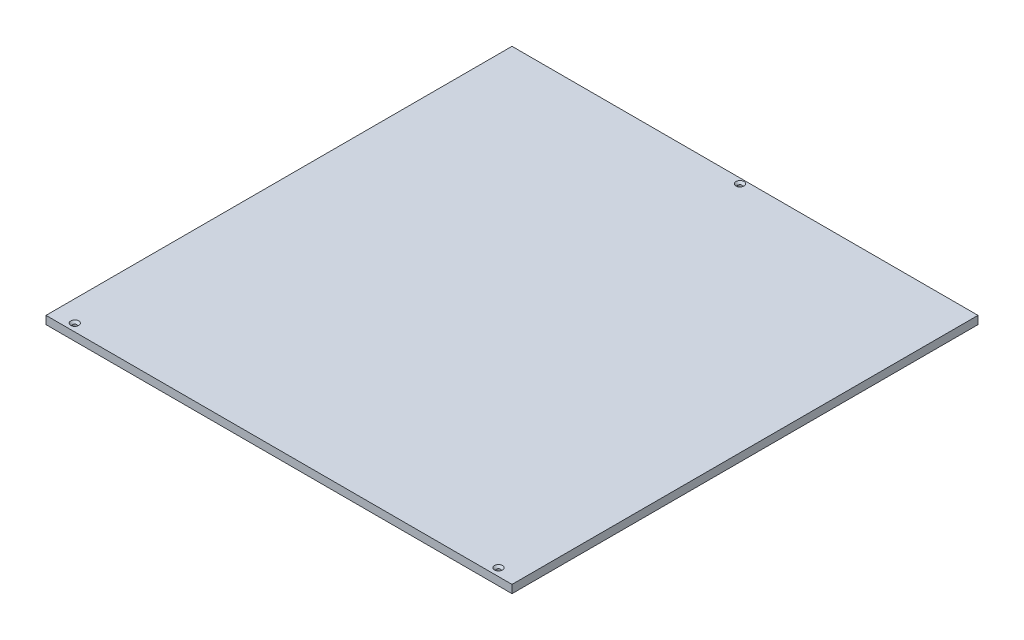
SolidWorks part; units mm, degrees
ref_plane "Front Plane" through (0, 0, 0) normal (0, 0, 1) x (1, 0, 0)
ref_plane "Top Plane" through (0, 0, 0) normal (0, 1, 0) x (1, 0, 0)
ref_plane "Right Plane" through (0, 0, 0) normal (1, 0, 0) x (0, 0, -1)
sketch "Sketch1" plane through (0, 0, 0) normal (0, 1, 0) x (1, 0, 0)
  line L0 (0, -121.6624) -> (0, 273.9976) construction
  line L1 (-255, -255) -> (255, -255) construction
  line L2 (-255, -255) -> (-255, 255) construction
  line L3 (-255, 255) -> (255, 255) construction
  line L4 (255, -255) -> (255, 255) construction
  line L5 (-255, -255) -> (255, 255) construction
  line L6 (-255, 255) -> (255, -255) construction
  line L7 (0, -121.6624) -> (250, -266) construction
  line L8 (0, -121.6624) -> (-250, -266) construction
  line L14 (255, -255) -> (245, -255)
  line L15 (255, -255) -> (255, -271)
  line L16 (255, -271) -> (245, -271)
  line L17 (245, -255) -> (245, -271)
  line L18 (-255, -255) -> (-245, -255)
  line L19 (-255, -255) -> (-255, -271)
  line L20 (-255, -271) -> (-245, -271)
  line L21 (-245, -255) -> (-245, -271)
  line L22 (-275, -275) -> (275, -275)
  line L23 (-275, -275) -> (-275, 275)
  line L24 (-275, 275) -> (275, 275)
  line L25 (275, -275) -> (275, 275)
  line L26 (-275, -275) -> (275, 275) construction
  line L27 (-275, 275) -> (275, -275) construction
  circle A0 centre (0, 0) radius 255 construction
  circle A1 centre (250, -266) radius 2.1
  circle A2 centre (0, 268.9976) radius 2.1
  circle A3 centre (-250, -266) radius 2.1
  dimension "D1" = 510
  dimension "D18" = 4.2
  dimension "D19" = 4.2
  dimension "D20" = 4.2
  dimension "D2" = 510
  dimension "D3" = 510
  dimension "D4" = 120
  dimension "D5" = 120
  dimension "D6" = 395.66
  dimension "D7" = 10
  dimension "D8" = 16
  dimension "D9" = 5
  dimension "D10" = 5
  dimension "D11" = 5
  dimension "D12" = 10
  dimension "D13" = 16
  dimension "D14" = 5
  dimension "D15" = 288.6751
  dimension "D16" = 550
  dimension "D17" = 550
extrude "Boss-Extrude1" add sketch "Sketch1" along normal blind 9.525 contours L22 L25 L24 L23 A2 L18 L21 L20 L19 L17 L14 L15 L16 | L21 L18 L19 L20 A3 | L14 L17 L16 L15 A1
hole_wizard "CSK for M4 Flat Head Machine Screw1" positions "Sketch2" profile "Sketch3" countersink size "M4" standard "ANSI Metric"
sketch "Sketch2" plane through (0, 9.525, 0) normal (0, 1, 0) x (1, 0, 0)
  point P0 (0, 268.9976)
  point P3 (250, -266)
  point P6 (-250, -266)
sketch "Sketch3" plane through (0, 9.525, -268.9976) normal (1, 0, 0) x (0, 0, 1)
  line L0 (0, 0) -> (0, 10.8819)
  line L1 (0, 10.8819) -> (2.25, 9.53)
  line L2 (2.25, 9.53) -> (2.25, 2.45)
  line L3 (2.25, 2.45) -> (4.7, 0)
  line L5 (4.7, 0) -> (0, 0)
  line L6 (-2.25, 2.45) -> (-4.7, 0) construction
  line L10 (0, 10.8819) -> (-2.25, 9.53) construction
  line L11 (0, -6.35) -> (0, 107.95) construction
  dimension "Hole Dia." = 4.5
  dimension "Hole Depth" = 9.53
  dimension "Near C'Sink Dia." = 9.4
  dimension "Near C'Sink Angle" = 90
  dimension "Drill Angle" = 118
